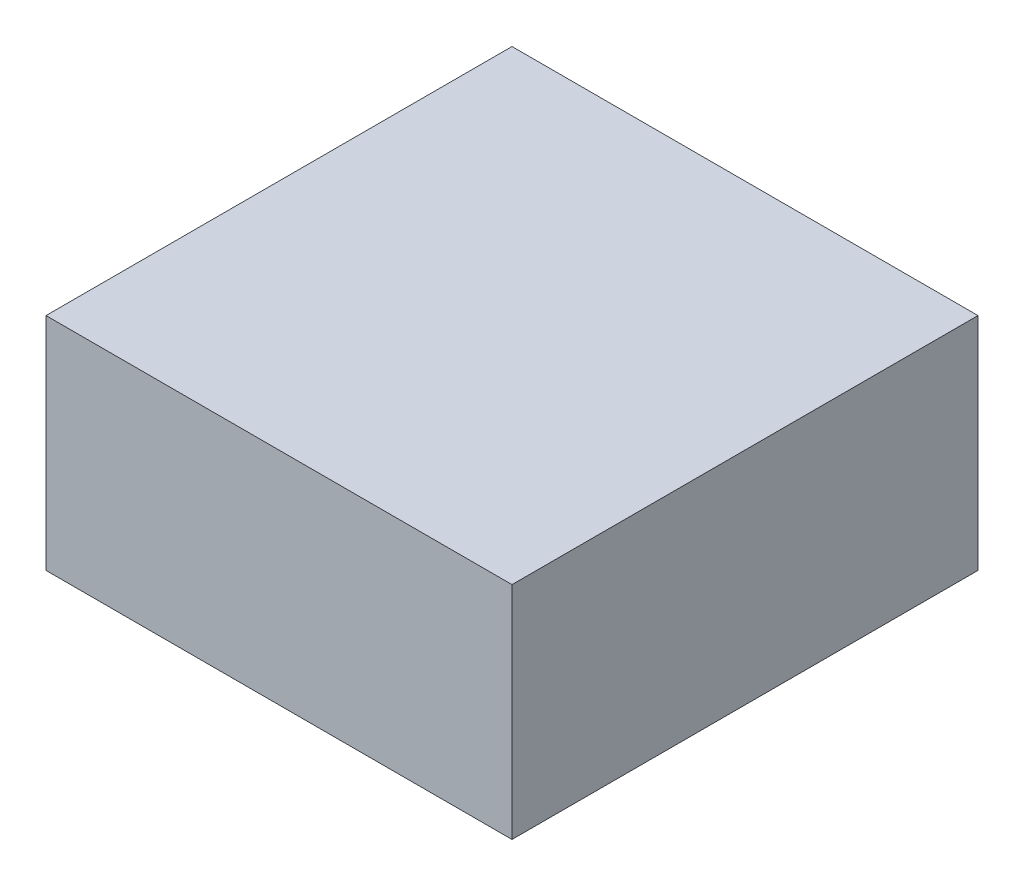
SolidWorks part; units mm, degrees
ref_plane "Front Plane" through (0, 0, 0) normal (0, 0, 1) x (1, 0, 0)
ref_plane "Top Plane" through (0, 0, 0) normal (0, 1, 0) x (1, 0, 0)
ref_plane "Right Plane" through (0, 0, 0) normal (1, 0, 0) x (0, 0, -1)
sketch "Sketch1" plane through (0, 0, 0) normal (0, 1, 0) x (1, 0, 0)
  line L1 (0, 0) -> (38, 0)
  line L2 (0, 0) -> (0, 38)
  line L3 (0, 38) -> (38, 38)
  line L4 (38, 0) -> (38, 38)
extrude "Boss-Extrude1" add sketch "Sketch1" along normal blind 18
sketch "Sketch2" plane through (0, 0, 0) normal (1, 0, 0) x (0, 0, -1)
  line L1 (38, 18) -> (38, 0) construction
  circle A1 centre (30, 9) radius 7
  circle A2 centre (30, 9) radius 6
  point P4 (38, 9)
  dimension "D1" = 8
